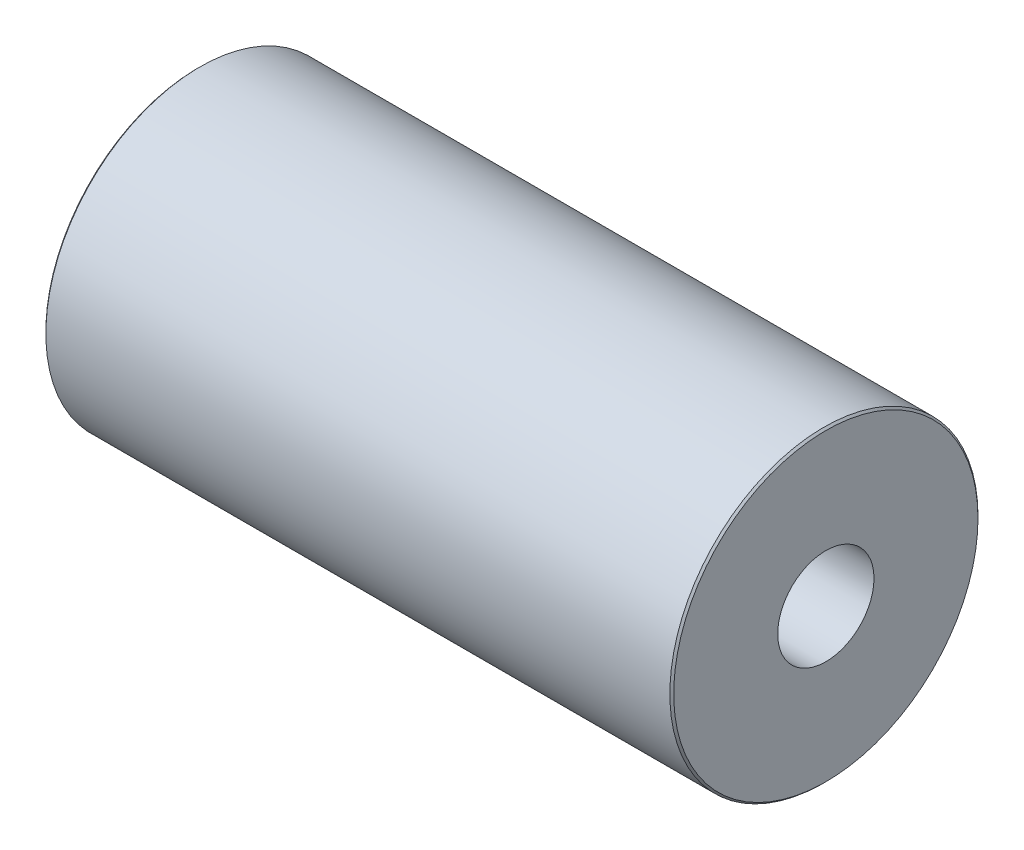
SolidWorks part; units mm, degrees
material "1.7225 (42CrMo4)"
ref_plane "前基準面" through (0, 0, 0) normal (0, 0, 1) x (1, 0, 0)
ref_plane "上基準面" through (0, 0, 0) normal (0, 1, 0) x (1, 0, 0)
ref_plane "右基準面" through (0, 0, 0) normal (1, 0, 0) x (0, 0, -1)
sketch "Sketch1" plane through (0, 0, 0) normal (1, 0, 0) x (0, 0, -1)
  circle A0 centre (0, 0) radius 8
  circle A1 centre (0, 0) radius 3
  dimension "D1" = 6
  dimension "D2" = 16
extrude "Boss-Extrude1" add sketch "Sketch1" along normal mid plane 32.6 contours A1 | A0 A1
hole_wizard "M6 Tapped Hole1" positions "Sketch2" profile "Sketch3" tap size "M6" standard "ISO"
sketch "Sketch2" plane through (-16.3, 0, 0) normal (-1, 0, 0) x (0, 0, 1)
  point P0 (0, 0)
sketch "Sketch3" plane through (-16.3, 0, 0) normal (0, 1, 0) x (0, 0, 1)
  line L0 (0, 0) -> (0, 11.5022)
  line L1 (0, 11.5022) -> (2.5, 10)
  line L2 (2.5, 10) -> (2.5, 0)
  line L5 (2.5, 0) -> (0, 0)
  line L10 (0, 11.5022) -> (-2.5, 10) construction
  line L11 (0, -6.35) -> (0, 107.95) construction
  dimension "Tap Drill Dia." = 5
  dimension "Tap Drill Depth" = 10
  dimension "Drill Angle" = 118
cosmetic thread "Hole Thread1" parameters "D1"=12, "D2"=6
mirror "Mirror1" about plane through (0, 0, 0) normal (1, 0, 0) of "M6 Tapped Hole1"
cosmetic thread "Hole Thread2" parameters "D1"=12, "D2"=6
chamfer "Chamfer1" distance 0.1 angle 45 2 edges at (-16.3, 0, -8) (16.3, 0, -8)
